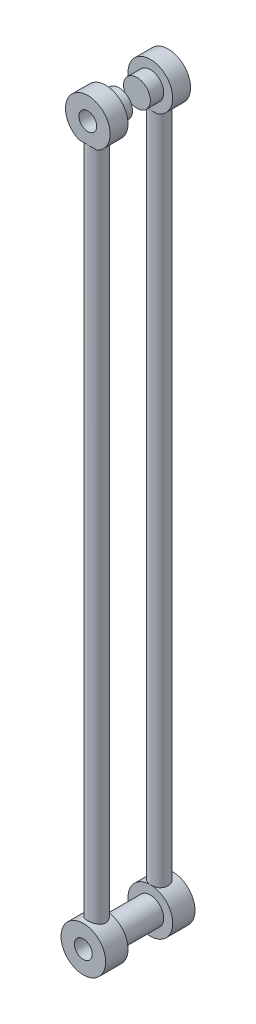
SolidWorks part; units mm, degrees
ref_plane "Front Plane" through (0, 0, 0) normal (0, 0, 1) x (1, 0, 0)
ref_plane "Top Plane" through (0, 0, 0) normal (0, 1, 0) x (1, 0, 0)
ref_plane "Right Plane" through (0, 0, 0) normal (1, 0, 0) x (0, 0, -1)
sketch "Sketch1" plane through (0, 0, 0) normal (0, 0, 1) x (1, 0, 0)
  line L0 (0, 0) -> (0, -400)
  circle A0 centre (0, 0) radius 5
  circle A1 centre (0, 0) radius 12.5
extrude "Boss-Extrude1" add sketch "Sketch1" along normal blind 10
sketch "Sketch2" plane through (0, 0, 10) normal (0, 0, 1) x (1, 0, 0)
  line L0 (0, 0) -> (0, -12)
  line L1 (0, -12) -> (9.1081, -12)
  line L2 (9.1081, -12) -> (-7.4949, -12)
  line L3 (-7.4949, -12) -> (-7.4949, -13.6285)
  line L4 (-7.4949, -13.6285) -> (9.5114, -13.6285)
  line L5 (9.5114, -13.6285) -> (9.1081, -12)
  circle M5 centre (0, 0) radius 12.5
extrude "Cut-Extrude2" cut sketch "Sketch2" against normal through all contours L4 L5 L1 L2 L3 M5 | L1 L2 M5
sketch "Sketch3" plane through (0, -12, 0) normal (0, -1, 0) x (-1, 0, 0)
  circle A0 centre (0, -5) radius 5
extrude "Boss-Extrude2" add sketch "Sketch3" along normal blind 188
mirror "Mirror2" about plane through (0, -200, 5) normal (0, -1, 0) of "Boss-Extrude2", "Boss-Extrude1"
sketch "Sketch5" plane through (0, 0, 0) normal (0, 0, 1) x (1, 0, 0)
  line L0 (0, 0) -> (0, -388)
  line L1 (-5, -388) -> (5, -388) construction
  line L2 (0, -388) -> (0, -400)
  circle A0 centre (0, -400) radius 5
  circle A1 centre (0, -400) radius 12.5
  dimension "D1" = 25
extrude "Boss-Extrude4" add sketch "Sketch5" along normal blind 10
sketch "Sketch7" plane through (0, 0, 10) normal (0, 0, 1) x (1, 0, 0)
  circle A0 centre (0, 0) radius 7.5
  circle A1 centre (0, -400) radius 7.5
  dimension "D1" = 15
  dimension "D2" = 15
extrude "Boss-Extrude5" add sketch "Sketch7" along normal blind 25 separate body
sketch "Sketch8" plane through (0, 0, 35) normal (0, 0, 1) x (1, 0, 0)
  circle A0 centre (0, 0) radius 12.5
  circle A1 centre (0, 0) radius 5
  circle A2 centre (0, -400) radius 5
  circle A3 centre (0, -400) radius 12.5
extrude "Boss-Extrude6" add sketch "Sketch8" along normal blind 10 separate body
sketch "Sketch9" plane through (0, 0, 45) normal (0, 0, 1) x (1, 0, 0)
  line L0 (0, 0) -> (0, -12.5)
  line L1 (-5, -12) -> (-5, -11.4564)
  line L2 (-5, -11.4564) -> (5, -11.4564)
  line L3 (5, -11.4564) -> (5, -13.442)
  line L4 (5, -13.442) -> (-5, -12)
  circle A1 centre (0, 0) radius 12.5 construction
  circle M1 centre (0, 0) radius 12.5
extrude "Cut-Extrude3" cut sketch "Sketch9" against normal blind 20 contours L2 L0 M1 | L2 L0 M1 | L4 L3 L1 M1
sketch "Sketch12" plane through (0, -11.4564, 0) normal (0, -1, 0) x (-1, 0, 0)
  circle A0 centre (0, -40) radius 5
extrude "Boss-Extrude8" add sketch "Sketch12" along normal blind 380
sketch "Sketch13" plane through (0, 0, 0) normal (1, 0, 0) x (0, 0, -1)
  line L0 (-22.5, 7.5) -> (-27.5, 7.5)
  line L1 (-10, 7.5) -> (-35, 7.5) construction
  line L2 (-27.5, 7.5) -> (-17.5, 7.5)
  line L3 (-17.5, 7.5) -> (-17.5, -15.8034)
  line L4 (-17.5, -15.8034) -> (-27.5, -15.8034)
  line L5 (-27.5, -15.8034) -> (-27.5, 7.5)
extrude "Cut-Extrude4" cut sketch "Sketch13" against normal through all both and the other way through all contours L5 L4 L3 L2 L0
sketch "Sketch14" plane through (0, 0, 45) normal (0, 0, 1) x (1, 0, 0)
  circle A0 centre (0, -400) radius 5
  circle A1 centre (0, -400) radius 12.5
extrude "Boss-Extrude9" add sketch "Sketch14" along normal blind 2.5
sketch "Sketch15" plane through (0, 0, 0) normal (0, 0, -1) x (-1, 0, 0)
  circle A0 centre (0, -400) radius 5
  circle A1 centre (0, -400) radius 12.5
extrude "Boss-Extrude10" add sketch "Sketch15" along normal blind 2.5
